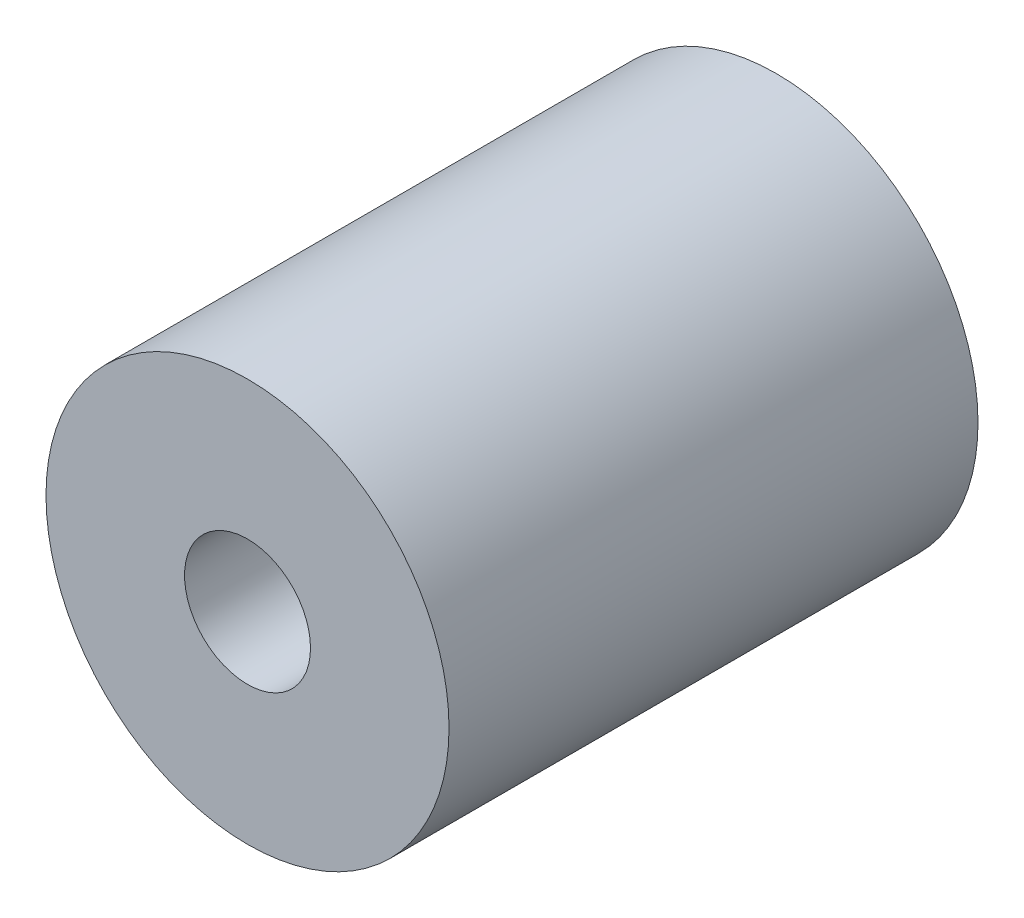
SolidWorks part; units mm, degrees
ref_plane "Płaszczyzna przednia" through (0, 0, 0) normal (0, 0, 1) x (1, 0, 0)
ref_plane "Płaszczyzna górna" through (0, 0, 0) normal (0, 1, 0) x (1, 0, 0)
ref_plane "Płaszczyzna prawa" through (0, 0, 0) normal (1, 0, 0) x (0, 0, -1)
sketch "Szkic1" plane through (0, 0, 0) normal (0, 0, 1) x (1, 0, 0)
  circle A0 centre (0, 0) radius 5
  circle A1 centre (0, 0) radius 16
extrude "Dodanie-wyciągnięcie1" add sketch "Szkic1" along normal blind 42
